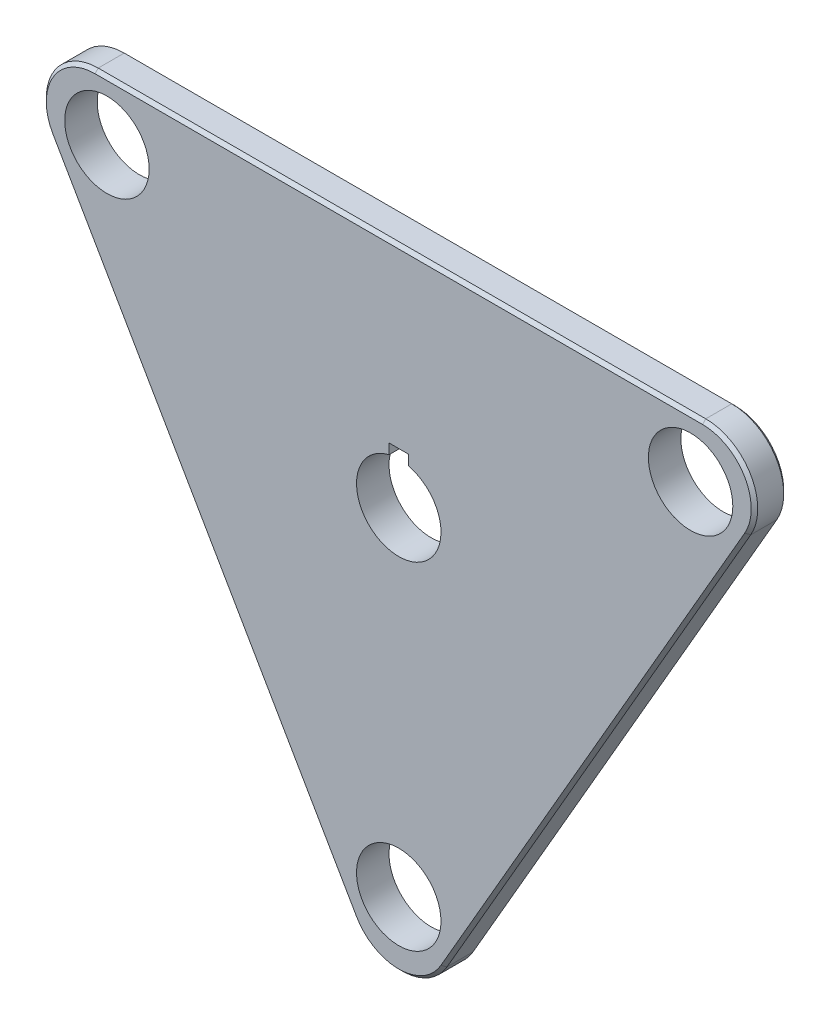
SolidWorks part; units mm, degrees
ref_plane "Front Plane" through (0, 0, 0) normal (0, 0, 1) x (1, 0, 0)
ref_plane "Top Plane" through (0, 0, 0) normal (0, 1, 0) x (1, 0, 0)
ref_plane "Right Plane" through (0, 0, 0) normal (1, 0, 0) x (0, 0, -1)
sketch "Sketch1" plane through (0, 0, 0) normal (0, 0, 1) x (1, 0, 0)
  line L0 (0, 0) -> (0, -51.88) construction
  line L1 (0, 0) -> (-44.9294, 25.94) construction
  line L2 (0, 0) -> (44.9294, 25.94) construction
  line L3 (0, 0) -> (0, -70) construction
  line L4 (0, 0) -> (-60.6218, 35) construction
  line L5 (0, 0) -> (60.6218, 35) construction
  line L6 (6.9282, -58) -> (53.6936, 23)
  line L7 (46.7654, 35) -> (-46.7654, 35)
  line L8 (-53.6936, 23) -> (-6.9282, -58)
  arc A0 (-46.7654, 35) -> (-53.6936, 23) centre (-46.7654, 27) ccw
  arc A1 (53.6936, 23) -> (46.7654, 35) centre (46.7654, 27) ccw
  arc A2 (-6.9282, -58) -> (6.9282, -58) centre (0, -54) ccw
  circle A3 centre (-44.9294, 25.94) radius 6.5
  circle A4 centre (44.9294, 25.94) radius 6.5
  circle A5 centre (0, -51.88) radius 6.5
  dimension "D7" = 8
  dimension "D8" = 8
  dimension "D9" = 8
  dimension "D10" = 13
  dimension "D1" = 51.88
  dimension "D2" = 51.88
  dimension "D3" = 51.88
  dimension "D4" = 70
  dimension "D5" = 70
  dimension "D6" = 70
extrude "Boss-Extrude1" add sketch "Sketch1" against normal blind 5
chamfer "Chamfer1" distance 0.5 angle 45 6 edges at (0, -62, 0) (30.3109, -17.5, 0) (-30.3109, -17.5, 0) (53.6936, 31, 0) (-53.6936, 31, 0) (0, 35, 0)
chamfer "Chamfer2" distance 0.5 angle 45 6 edges at (0, -62, -5) (30.3109, -17.5, -5) (-30.3109, -17.5, -5) (53.6936, 31, -5) (-53.6936, 31, -5) (0, 35, -5)
sketch "Sketch2" plane through (0, 0, 0) normal (0, 0, 1) x (1, 0, 0)
  circle A0 centre (0, 0) radius 6.5
  dimension "D1" = 13
extrude "Cut-Extrude1" cut sketch "Sketch2" against normal through all
sketch "Sketch3" plane through (0, 0, 0) normal (0, 0, 1) x (1, 0, 0)
  line L0 (0, 0) -> (0, 6.5) construction
  line L1 (-1.5, 6.5) -> (1.5, 6.5) construction
  line L2 (-1.5, 6.5) -> (-1.5, 7.9)
  line L3 (-1.5, 7.9) -> (1.5, 7.9)
  line L4 (1.5, 6.5) -> (1.5, 7.9)
  line L5 (-1.5, 6.5) -> (-1.5, 6.2248)
  line L6 (-1.5, 6.2248) -> (1.5, 6.2248)
  line L7 (1.5, 6.2248) -> (1.5, 6.5)
  circle A0 centre (0, 0) radius 6.5 construction
  point P10 (0, 7.9)
extrude "Cut-Extrude2" cut sketch "Sketch3" against normal blind 10
equation "\"glo\"=22.0159"
equation "\"global\"=51.88"
equation "\"planet\"=51.88"
equation "\"D1@Sketch1\"=\"planet\""
equation "\"D2@Sketch1\"=\"global\""
equation "\"D3@Sketch1\"=\"global\""
equation "\"carrier\"=70"
equation "\"D4@Sketch1\"=\"carrier\""
equation "\"D5@Sketch1\"=\"carrier\""
equation "\"D6@Sketch1\"=\"carrier\""
equation "\"radius\"=13"
equation "\"D10@Sketch1\"=\"radius\""
